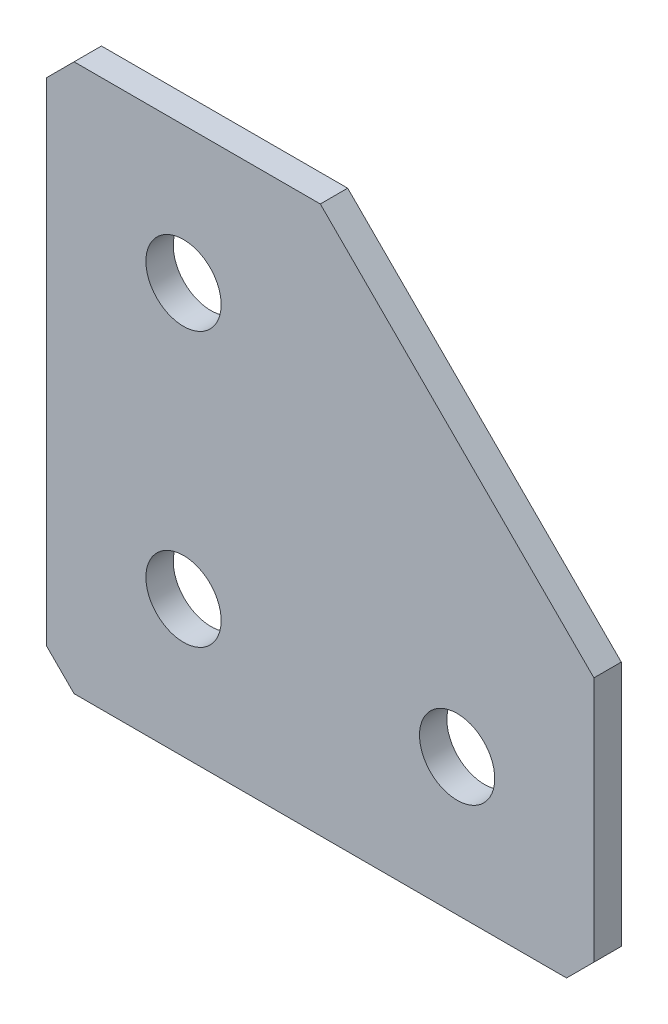
SolidWorks part; units mm, degrees
material "Простая углеродистая сталь"
ref_plane "Спереди(Плоскость XY)" through (0, 0, 0) normal (0, 0, 1) x (1, 0, 0)
ref_plane "Сверху(Плоскость XZ)" through (0, 0, 0) normal (0, 1, 0) x (1, 0, 0)
ref_plane "Справа(Плоскость ZY)" through (0, 0, 0) normal (1, 0, 0) x (0, 0, -1)
sketch "Эскиз1" plane through (0, 0, 0) normal (0, 0, -1) x (1, 0, 0)
  line L0 (0, 0) -> (0, 40)
  line L1 (0, 40) -> (40, 40)
  line L2 (40, 40) -> (40, 20)
  line L3 (40, 20) -> (20, 20) construction
  line L4 (20, 20) -> (20, 0) construction
  line L5 (20, 0) -> (0, 0)
  line L6 (40, 20) -> (20, 0)
  dimension "D1" = 40
  dimension "D2" = 20
  dimension "D3" = 20
  dimension "D4" = 20
extrude "Бобышка-Вытянуть1" add sketch "Эскиз1" along normal blind 2
hole_wizard "Отверстие с зазором M51" positions "Эскиз2" profile "Эскиз3" hole size "M5" standard "DIN" end condition through all
sketch "Эскиз2" plane through (0, 0, -2) normal (0, 0, -1) x (1, 0, 0)
  line L0 (10, 0) -> (10, 40) construction
  line L1 (0, 0) -> (20, 0) construction
  line L2 (40, 40) -> (0, 40) construction
  line L3 (40, 30) -> (0, 30) construction
  line L4 (40, 20) -> (40, 40) construction
  line L5 (0, 40) -> (0, 0) construction
  point P0 (10, 30)
  point P4 (10, 30)
  point P6 (10, 10)
  point P21 (30, 30)
  dimension "D1" = 20
  dimension "D2" = 20
  dimension "D4" = 10
sketch "Эскиз3" plane through (10, -30, -2) normal (1, 0, 0) x (0, 1, 0)
  line L0 (0, 0) -> (0, 2)
  line L1 (0, 2) -> (2.75, 2)
  line L2 (2.75, 2) -> (2.75, 0)
  line L5 (2.75, 0) -> (0, 0)
  line L11 (0, -6.35) -> (0, 107.95) construction
  dimension "Диаметр сквозного отверстия" = 5.5
  dimension "Глубина сквозного отверстия" = 2
chamfer "Фаска1" distance 2 angle 45 3 edges at (0, 0, -1) (40, -40, -1) (0, -40, -1)
